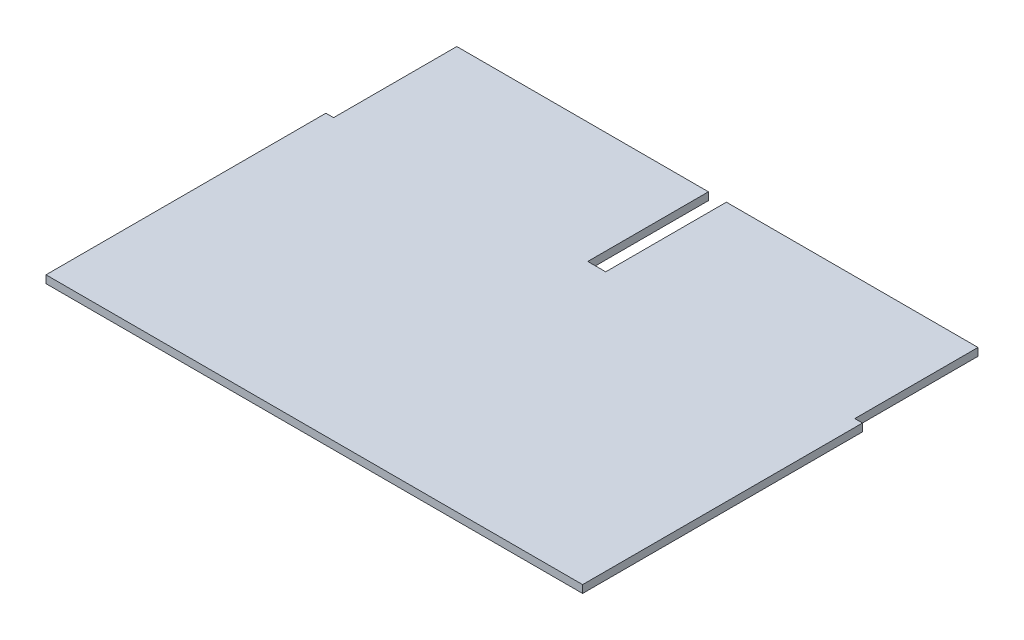
SolidWorks part; units mm, degrees
ref_plane "Front Plane" through (0, 0, 0) normal (0, 0, 1) x (1, 0, 0)
ref_plane "Top Plane" through (0, 0, 0) normal (0, 1, 0) x (1, 0, 0)
ref_plane "Right Plane" through (0, 0, 0) normal (1, 0, 0) x (0, 0, -1)
sketch "Sketch1" plane through (0, 0, 0) normal (0, 1, 0) x (1, 0, 0)
  line L0 (0, 15.8) -> (0, -15.8) construction
  line L1 (-10.55, -15.8) -> (10.55, -15.8)
  line L2 (-10.55, -15.8) -> (-10.55, 15.8)
  line L3 (-10.55, 15.8) -> (10.55, 15.8)
  line L4 (10.55, -15.8) -> (10.55, 15.8)
  line L5 (-10.55, -15.8) -> (10.55, 15.8) construction
  line L6 (-10.55, 15.8) -> (10.55, -15.8) construction
  line L7 (-10.25, 15.8) -> (-10.25, -15.8)
  line L8 (10.25, 15.8) -> (10.25, -15.8)
  line L9 (-10.55, 11) -> (10.55, 11)
  line L10 (-0.25, 15.8) -> (-0.25, 11)
  line L11 (0.25, 15.8) -> (0.25, 11)
  line L12 (-10.55, 0) -> (10.55, 0)
  line L13 (-10.45, -15.7) -> (-10.45, 15.7)
  line L14 (-10.45, 15.7) -> (10.45, 15.7)
  line L15 (10.45, -15.7) -> (10.45, 15.7)
  line L16 (-10.45, -15.7) -> (10.45, -15.7)
  line L17 (-0.35, 15.8) -> (-0.35, 11)
  line L18 (-10.55, 10.9) -> (10.55, 10.9)
  line L19 (0.35, 15.8) -> (0.35, 11)
  line L20 (-0.35, 11) -> (-0.35, 10.9)
  line L21 (0.35, 11) -> (0.35, 10.9)
  line L22 (-10.15, 15.8) -> (-10.15, -15.8)
  line L23 (10.15, 15.8) -> (10.15, -15.8)
  point P0 (0, 0)
  point P9 (-10.25, 15.8)
  point P14 (-10.55, 11)
  point P17 (-0.25, 15.8)
  dimension "D1" = 0.1
  dimension "D2" = 0.1
  dimension "D3" = 0.1
  dimension "D4" = 0.1
extrude "Boss-Extrude1" add sketch "Sketch1" along normal blind 0.3 contours L14 L22 L9 L17 | L23 L14 L19 L9 | L9 L22 L18 L20 | L23 L9 L21 L18 | L21 L9 L20 L18 | L23 L18 L22 L12 | L22 L18 L7 L12 | L18 L13 L12 L7 | L18 L8 L12 L15 | L18 L23 L12 L8
